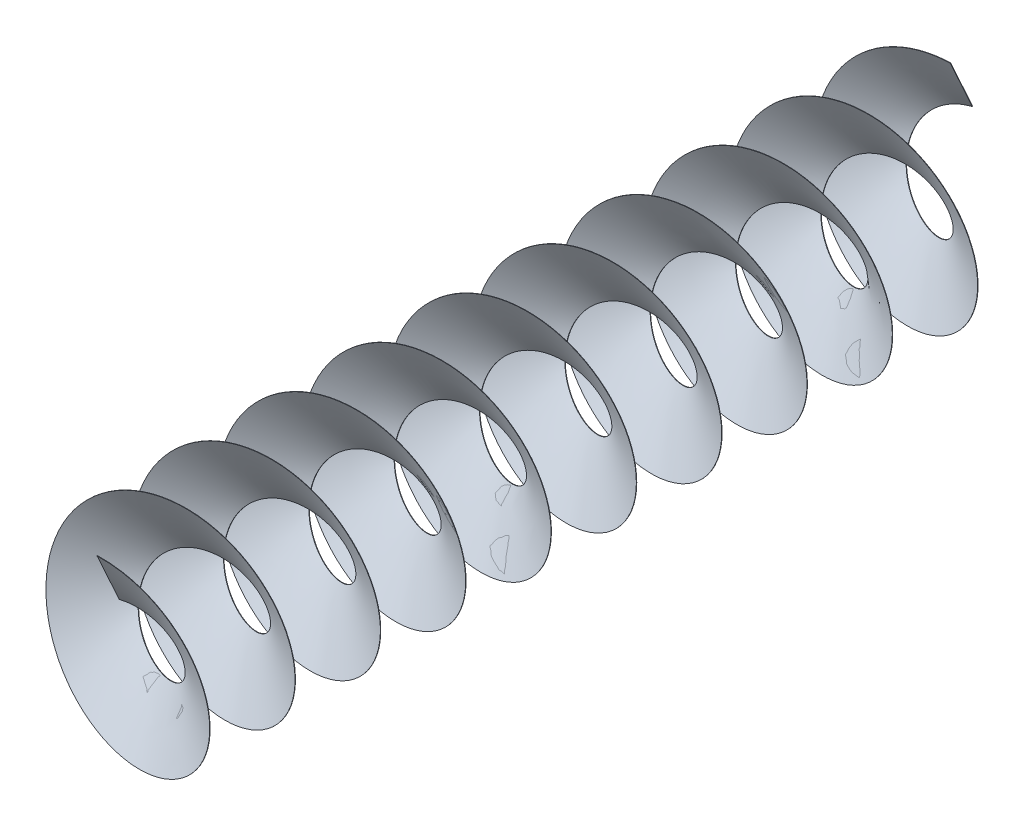
SolidWorks part; units mm, degrees
material "Unlegierter Baustahl"
ref_plane "Ebene vorne" through (0, 0, 0) normal (0, 0, 1) x (1, 0, 0)
ref_plane "Ebene oben" through (0, 0, 0) normal (0, 1, 0) x (1, 0, 0)
ref_plane "Ebene rechts" through (0, 0, 0) normal (1, 0, 0) x (0, 0, -1)
sketch "Skizze1" plane through (0, 0, 0) normal (0, 0, 1) x (1, 0, 0)
  circle A0 centre (0, 0) radius 25
  dimension "D1" = 50
curve "Spirale/Helix1" pitch 50 height 500 turns 10
ref_plane "Ebene1" through (0, 25, 0) normal (0.9529, 0, -0.3033) x (-0.3033, 0, -0.9529)
sketch "Skizze2" plane through (0, 25, 0) normal (0.9529, 0, -0.3033) x (-0.3033, 0, -0.9529)
  line L0 (0, 0) -> (-0.25, 0)
  line L1 (0, 0) -> (-20, 34.641)
  line L2 (-0.25, 0) -> (-20.25, 34.641)
  line L3 (-20, 34.641) -> (-20.25, 34.641)
  dimension "D1" = 0.25
  dimension "D2" = 60
  dimension "D3" = 40
sweep "Austragung1" add profiles "Skizze2" path "Spirale/Helix1"
